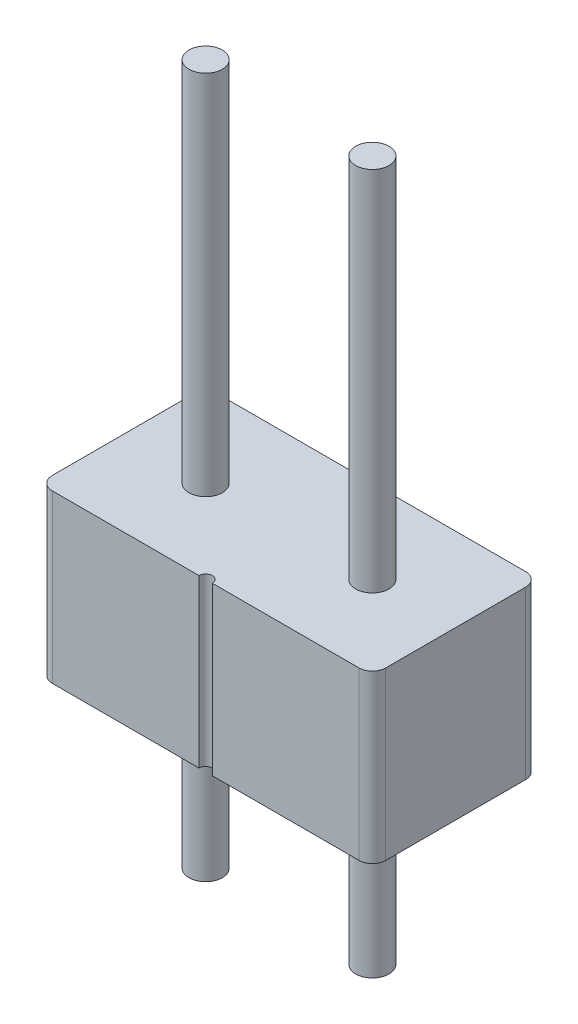
SolidWorks part; units mm, degrees
ref_plane "Ön Düzlem" through (0, 0, 0) normal (0, 0, 1) x (1, 0, 0)
ref_plane "Üst Düzlem" through (0, 0, 0) normal (0, 1, 0) x (1, 0, 0)
ref_plane "Sağ Düzlem" through (0, 0, 0) normal (1, 0, 0) x (0, 0, -1)
sketch "Çizim1" plane through (0, 0, 0) normal (0, 1, 0) x (1, 0, 0)
  line L1 (-2.3, 1.25) -> (-0.1, 1.25)
  line L2 (-2.5, 1.05) -> (-2.5, -1.05)
  line L3 (-2.3, -1.25) -> (-0.1, -1.25)
  line L4 (2.5, 1.05) -> (2.5, -1.05)
  line L5 (-2.5, 1.25) -> (2.5, -1.25) construction
  line L6 (-2.5, -1.25) -> (2.5, 1.25) construction
  line L8 (-1.25, 1.25) -> (-1.25, -1.25) construction
  line L9 (1.25, 1.25) -> (1.25, -1.25) construction
  line L10 (-2.5, 0) -> (2.5, 0) construction
  line L11 (0.1, 1.25) -> (2.3, 1.25)
  line L12 (0.1, -1.25) -> (2.3, -1.25)
  circle A0 centre (-1.25, 0) radius 0.25
  circle A1 centre (1.25, 0) radius 0.25
  arc A2 (-0.1, 1.25) -> (0.1, 1.25) centre (0, 1.25) ccw
  arc A3 (0.1, -1.25) -> (-0.1, -1.25) centre (0, -1.25) ccw
  arc A4 (2.3, -1.25) -> (2.5, -1.05) centre (2.3, -1.05) ccw
  arc A5 (2.3, 1.25) -> (2.5, 1.05) centre (2.3, 1.05) cw
  arc A6 (-2.5, -1.05) -> (-2.3, -1.25) centre (-2.3, -1.05) ccw
  arc A7 (-2.3, 1.25) -> (-2.5, 1.05) centre (-2.3, 1.05) ccw
  point P0 (0, 0)
  dimension "D5" = 0.5
  dimension "D6" = 0.2
  dimension "D7" = 0.2
  dimension "D1" = 2.5
  dimension "D2" = 5
  dimension "D3" = 1.25
extrude "Yükseklik-Ekstrüzyon1" add sketch "Çizim1" along normal blind 2.5
sketch "Çizim2" plane through (0, 2.5, 0) normal (0, 1, 0) x (1, 0, 0)
  circle A0 centre (-1.25, 0) radius 0.25
  circle A1 centre (1.25, 0) radius 0.25
extrude "Yükseklik-Ekstrüzyon2" add sketch "Çizim2" along normal blind 5.5 and the other way blind 5
